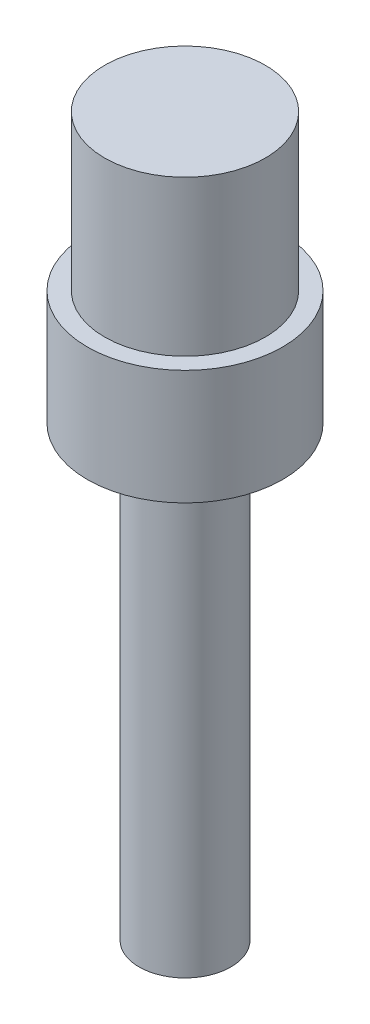
SolidWorks part; units mm, degrees
material "Latão"
ref_plane "Plano frontal" through (0, 0, 0) normal (0, 0, 1) x (1, 0, 0)
ref_plane "Plano superior" through (0, 0, 0) normal (0, 1, 0) x (1, 0, 0)
ref_plane "Plano direito" through (0, 0, 0) normal (1, 0, 0) x (0, 0, -1)
sketch "Esboço1" plane through (0, 0, 0) normal (0, 1, 0) x (1, 0, 0)
  circle A0 centre (0, 0) radius 8.5
  dimension "D1" = 17
extrude "Ressalto-extrusão1" add sketch "Esboço1" along normal blind 10
sketch "Esboço2" plane through (0, 10, 0) normal (0, 1, 0) x (1, 0, 0)
  circle A0 centre (0, 0) radius 7
  dimension "D1" = 14
extrude "Ressalto-extrusão2" add sketch "Esboço2" along normal blind 13.5
sketch "Esboço3" plane through (0, 0, 0) normal (0, -1, 0) x (1, 0, 0)
  circle A0 centre (0, 0) radius 4
  dimension "D1" = 8
extrude "Ressalto-extrusão3" add sketch "Esboço3" along normal blind 39
